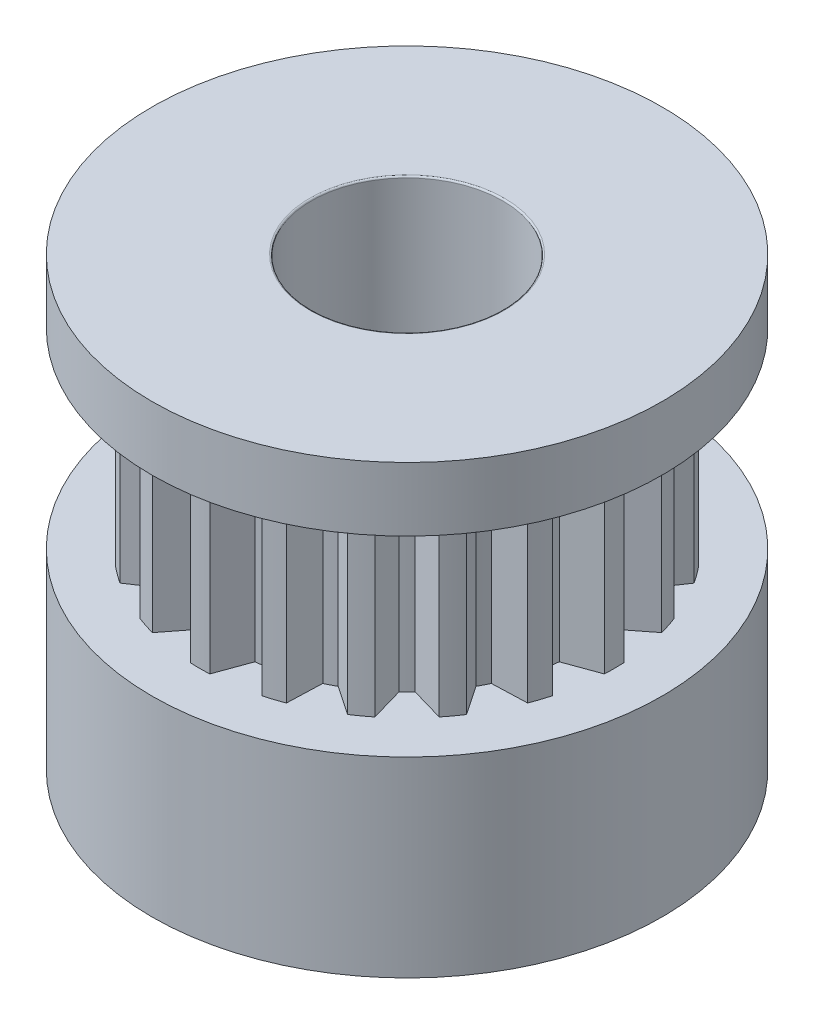
SolidWorks part; units mm, degrees
ref_plane "Front Plane" through (0, 0, 0) normal (0, 0, 1) x (1, 0, 0)
ref_plane "Top Plane" through (0, 0, 0) normal (0, 1, 0) x (1, 0, 0)
ref_plane "Right Plane" through (0, 0, 0) normal (1, 0, 0) x (0, 0, -1)
sketch "Sketch1" plane through (0, 0, 0) normal (0, 1, 0) x (1, 0, 0)
  circle A0 centre (0, 0) radius 8
  dimension "D1" = 16
extrude "Boss-Extrude1" add sketch "Sketch1" against normal blind 6
sketch "Sketch2" plane through (0, 0, 0) normal (0, 1, 0) x (1, 0, 0)
  line L0 (-6, 0) -> (6, 0) construction
  line L1 (0, 6) -> (0, -6) construction
  line L2 (0, 6) -> (0, 7) construction
  line L3 (-0.3059, 6.4928) -> (-0.6828, 5.4575)
  line L4 (0.3059, 6.4928) -> (0.6828, 5.4575)
  line L5 (1.7154, 6.2696) -> (1.0371, 5.4013)
  line L6 (2.2973, 6.0805) -> (2.3358, 4.9794)
  line L7 (3.5689, 5.4326) -> (2.6554, 4.8165)
  line L8 (4.0639, 5.073) -> (3.7602, 4.0139)
  line L9 (5.073, 4.0639) -> (4.0139, 3.7602)
  line L10 (5.4326, 3.5689) -> (4.8165, 2.6554)
  line L11 (6.0805, 2.2973) -> (4.9794, 2.3358)
  line L12 (6.2696, 1.7154) -> (5.4013, 1.0371)
  line L13 (6.4928, 0.3059) -> (5.4575, 0.6828)
  line L14 (6.4928, -0.3059) -> (5.4575, -0.6828)
  line L15 (6.2696, -1.7154) -> (5.4013, -1.0371)
  line L16 (6.0805, -2.2973) -> (4.9794, -2.3358)
  line L17 (5.4326, -3.5689) -> (4.8165, -2.6554)
  line L18 (5.073, -4.0639) -> (4.0139, -3.7602)
  line L19 (4.0639, -5.073) -> (3.7602, -4.0139)
  line L20 (3.5689, -5.4326) -> (2.6554, -4.8165)
  line L21 (2.2973, -6.0805) -> (2.3358, -4.9794)
  line L22 (1.7154, -6.2696) -> (1.0371, -5.4013)
  line L23 (0.3059, -6.4928) -> (0.6828, -5.4575)
  line L24 (-0.3059, -6.4928) -> (-0.6828, -5.4575)
  line L25 (-1.7154, -6.2696) -> (-1.0371, -5.4013)
  line L26 (-2.2973, -6.0805) -> (-2.3358, -4.9794)
  line L27 (-3.5689, -5.4326) -> (-2.6554, -4.8165)
  line L28 (-4.0639, -5.073) -> (-3.7602, -4.0139)
  line L29 (-5.073, -4.0639) -> (-4.0139, -3.7602)
  line L30 (-5.4326, -3.5689) -> (-4.8165, -2.6554)
  line L31 (-6.0805, -2.2973) -> (-4.9794, -2.3358)
  line L32 (-6.2696, -1.7154) -> (-5.4013, -1.0371)
  line L33 (-6.4928, -0.3059) -> (-5.4575, -0.6828)
  line L34 (-6.4928, 0.3059) -> (-5.4575, 0.6828)
  line L35 (-6.2696, 1.7154) -> (-5.4013, 1.0371)
  line L36 (-6.0805, 2.2973) -> (-4.9794, 2.3358)
  line L37 (-5.4326, 3.5689) -> (-4.8165, 2.6554)
  line L38 (-5.073, 4.0639) -> (-4.0139, 3.7602)
  line L39 (-4.0639, 5.073) -> (-3.7602, 4.0139)
  line L40 (-3.5689, 5.4326) -> (-2.6554, 4.8165)
  line L41 (-2.2973, 6.0805) -> (-2.3358, 4.9794)
  line L42 (-1.7154, 6.2696) -> (-1.0371, 5.4013)
  circle A0 centre (0, 0) radius 6 construction
  arc A1 (-1.7154, 6.2696) -> (-2.2973, 6.0805) centre (0, 0) ccw
  arc A2 (-2.3358, 4.9794) -> (-2.6554, 4.8165) centre (0, 0) ccw
  arc A3 (0.3059, 6.4928) -> (-0.3059, 6.4928) centre (0, 0) ccw
  circle A4 centre (0, 0) radius 6.5 construction
  arc A5 (2.2973, 6.0805) -> (1.7154, 6.2696) centre (0, 0) ccw
  arc A6 (4.0639, 5.073) -> (3.5689, 5.4326) centre (0, 0) ccw
  arc A7 (5.4326, 3.5689) -> (5.073, 4.0639) centre (0, 0) ccw
  arc A8 (6.2696, 1.7154) -> (6.0805, 2.2973) centre (0, 0) ccw
  arc A9 (6.4928, -0.3059) -> (6.4928, 0.3059) centre (0, 0) ccw
  arc A10 (6.0805, -2.2973) -> (6.2696, -1.7154) centre (0, 0) ccw
  arc A11 (5.073, -4.0639) -> (5.4326, -3.5689) centre (0, 0) ccw
  arc A12 (3.5689, -5.4326) -> (4.0639, -5.073) centre (0, 0) ccw
  arc A13 (1.7154, -6.2696) -> (2.2973, -6.0805) centre (0, 0) ccw
  arc A14 (-0.3059, -6.4928) -> (0.3059, -6.4928) centre (0, 0) ccw
  arc A15 (-2.2973, -6.0805) -> (-1.7154, -6.2696) centre (0, 0) ccw
  arc A16 (-4.0639, -5.073) -> (-3.5689, -5.4326) centre (0, 0) ccw
  arc A17 (-5.4326, -3.5689) -> (-5.073, -4.0639) centre (0, 0) ccw
  arc A18 (-6.2696, -1.7154) -> (-6.0805, -2.2973) centre (0, 0) ccw
  arc A19 (-6.4928, 0.3059) -> (-6.4928, -0.3059) centre (0, 0) ccw
  arc A20 (-6.0805, 2.2973) -> (-6.2696, 1.7154) centre (0, 0) ccw
  arc A21 (-5.073, 4.0639) -> (-5.4326, 3.5689) centre (0, 0) ccw
  arc A22 (-3.5689, 5.4326) -> (-4.0639, 5.073) centre (0, 0) ccw
  arc A23 (-0.6828, 5.4575) -> (-1.0371, 5.4013) centre (0, 0) ccw
  circle A24 centre (0, 0) radius 5.5 construction
  arc A25 (1.0371, 5.4013) -> (0.6828, 5.4575) centre (0, 0) ccw
  arc A26 (2.6554, 4.8165) -> (2.3358, 4.9794) centre (0, 0) ccw
  arc A27 (4.0139, 3.7602) -> (3.7602, 4.0139) centre (0, 0) ccw
  arc A28 (4.9794, 2.3358) -> (4.8165, 2.6554) centre (0, 0) ccw
  arc A29 (5.4575, 0.6828) -> (5.4013, 1.0371) centre (0, 0) ccw
  arc A30 (5.4013, -1.0371) -> (5.4575, -0.6828) centre (0, 0) ccw
  arc A31 (4.8165, -2.6554) -> (4.9794, -2.3358) centre (0, 0) ccw
  arc A32 (3.7602, -4.0139) -> (4.0139, -3.7602) centre (0, 0) ccw
  arc A33 (2.3358, -4.9794) -> (2.6554, -4.8165) centre (0, 0) ccw
  arc A34 (0.6828, -5.4575) -> (1.0371, -5.4013) centre (0, 0) ccw
  arc A35 (-1.0371, -5.4013) -> (-0.6828, -5.4575) centre (0, 0) ccw
  arc A36 (-2.6554, -4.8165) -> (-2.3358, -4.9794) centre (0, 0) ccw
  arc A37 (-4.0139, -3.7602) -> (-3.7602, -4.0139) centre (0, 0) ccw
  arc A38 (-4.9794, -2.3358) -> (-4.8165, -2.6554) centre (0, 0) ccw
  arc A39 (-5.4575, -0.6828) -> (-5.4013, -1.0371) centre (0, 0) ccw
  arc A40 (-5.4013, 1.0371) -> (-5.4575, 0.6828) centre (0, 0) ccw
  arc A41 (-4.8165, 2.6554) -> (-4.9794, 2.3358) centre (0, 0) ccw
  arc A42 (-3.7602, 4.0139) -> (-4.0139, 3.7602) centre (0, 0) ccw
  point P8 (4.5, 0)
  point P13 (5.5, 0)
  point P95 (0, 0)
  dimension "D1" = 12
  dimension "D4" = 1
  dimension "D5" = 20
  dimension "D6" = 20
  dimension "D2" = 0.5
  dimension "D3" = 0.5
  dimension "D7" = 20
extrude "Boss-Extrude2" add sketch "Sketch2" along normal blind 6
sketch "Sketch3" plane through (0, 6, 0) normal (0, 1, 0) x (1, 0, 0)
  circle A0 centre (0, 0) radius 8 construction
  circle A1 centre (0, 0) radius 8
extrude "Boss-Extrude3" add sketch "Sketch3" along normal blind 2
sketch "Sketch4" plane through (0, -6, 0) normal (0, -1, 0) x (1, 0, 0)
  circle A0 centre (0, 0) radius 3
  dimension "D1" = 6
extrude "Cut-Extrude1" cut sketch "Sketch4" against normal through all
sketch "Sketch5" plane through (0, -6, 0) normal (0, -1, 0) x (1, 0, 0)
  circle A0 centre (0, 0) radius 4
  dimension "D1" = 8
extrude "Cut-Extrude2" cut sketch "Sketch5" against normal blind 0.3
fillet "Fillet1" radius 0.05 2 edges at (0, 8, -3) (0, -5.7, -3)
